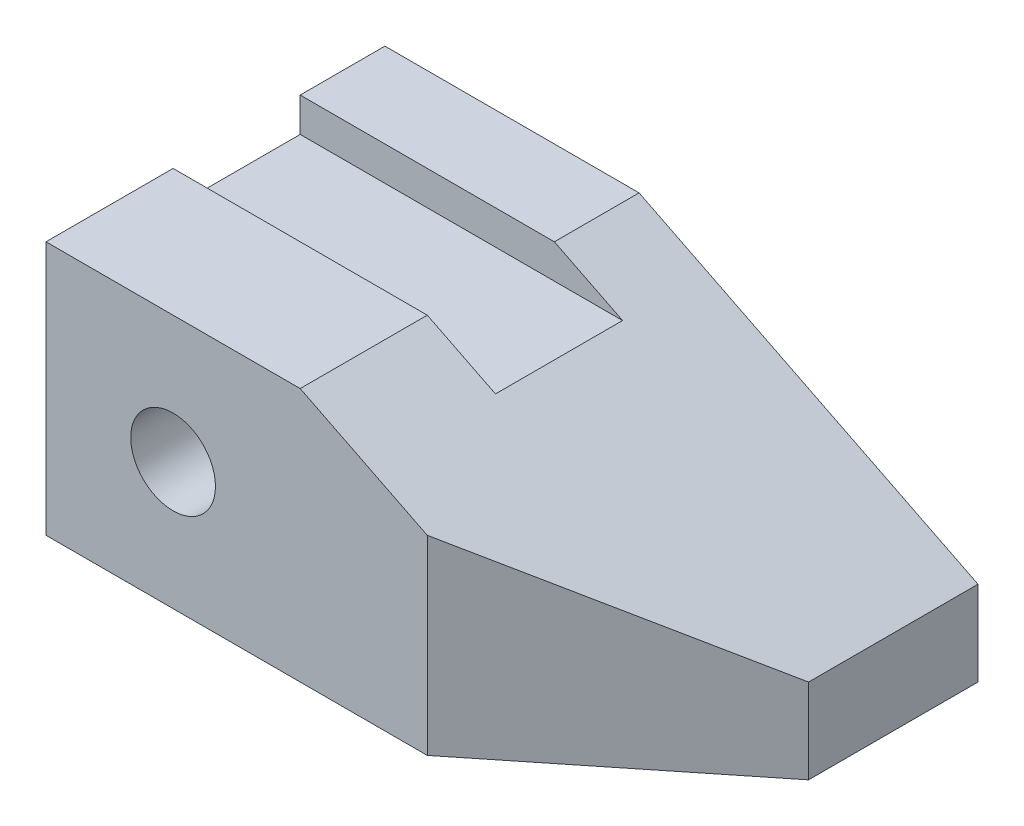
SolidWorks part; units mm, degrees
ref_plane "Front Plane" through (0, 0, 0) normal (0, 0, 1) x (1, 0, 0)
ref_plane "Top Plane" through (0, 0, 0) normal (0, 1, 0) x (1, 0, 0)
ref_plane "Right Plane" through (0, 0, 0) normal (1, 0, 0) x (0, 0, -1)
sketch "Sketch1" plane through (0, 0, 0) normal (0, 1, 0) x (1, 0, 0)
  line L1 (0, 0) -> (70, 0)
  line L2 (0, 0) -> (0, 40)
  line L3 (0, 40) -> (70, 40)
  line L4 (70, 0) -> (70, 40)
  dimension "D1" = 70
  dimension "D2" = 40
extrude "Boss-Extrude1" add sketch "Sketch1" along normal blind 30
sketch "Sketch2" plane through (0, 0, 0) normal (0, 0, 1) x (1, 0, 0)
  line L0 (70, 30) -> (30, 30)
  line L1 (0, 30) -> (70, 30) construction
  line L2 (30, 30) -> (70, 10)
  line L3 (70, 30) -> (70, 0) construction
  line L4 (70, 10) -> (70, 30)
  dimension "D1" = 20
  dimension "D2" = 40
extrude "Cut-Extrude1" cut sketch "Sketch2" against normal through all
sketch "Sketch3" plane through (0, 0, 0) normal (0, -1, 0) x (-1, 0, 0)
  line L0 (-70, 0) -> (-45, 0)
  line L1 (0, 0) -> (-70, 0) construction
  line L2 (-45, 0) -> (-70, 20)
  line L3 (-70, 0) -> (-70, 40) construction
  line L4 (-70, 20) -> (-70, 0)
  dimension "D1" = 25
  dimension "D2" = 20
extrude "Cut-Extrude2" cut sketch "Sketch3" against normal through all
sketch "Sketch4" plane through (0, 0, 0) normal (-1, 0, 0) x (0, 0, 1)
  line L0 (-40, 30) -> (-30, 30) construction
  line L1 (-40, 30) -> (0, 30) construction
  line L3 (-30, 30) -> (-15, 30)
  line L4 (-30, 30) -> (-30, 25.9755)
  line L5 (-30, 25.9755) -> (-15, 25.9755)
  line L6 (-15, 30) -> (-15, 25.9755)
  dimension "D1" = 10
  dimension "D2" = 15
extrude "Cut-Extrude3" cut sketch "Sketch4" against normal through all
sketch "Sketch5" plane through (0, 0, 0) normal (0, 0, 1) x (1, 0, 0)
  line L0 (0, 0) -> (15, 0) construction
  line L1 (0, 0) -> (45, 0) construction
  line L2 (15, 0) -> (15, 15) construction
  circle A0 centre (15, 15) radius 5
  dimension "D2" = 10
  dimension "D1" = 15
extrude "Cut-Extrude4" cut sketch "Sketch5" against normal through all
